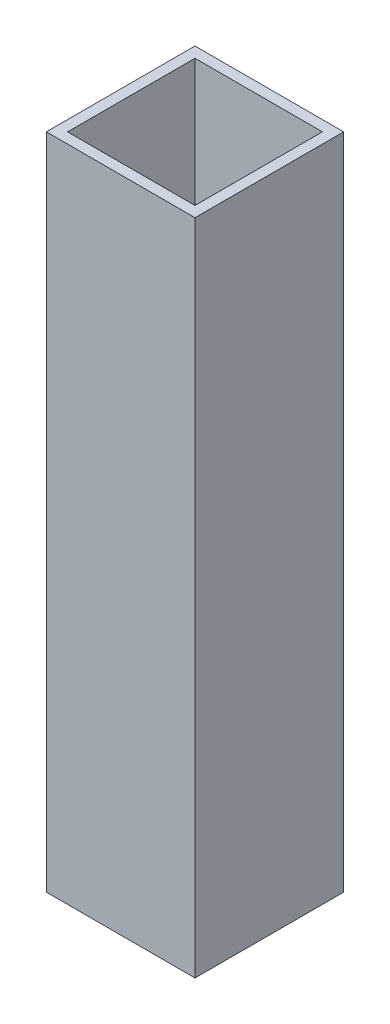
SolidWorks part; units mm, degrees
material "6063-T6"
ref_plane "Front Plane" through (0, 0, 0) normal (0, 0, 1) x (1, 0, 0)
ref_plane "Top Plane" through (0, 0, 0) normal (0, 1, 0) x (1, 0, 0)
ref_plane "Right Plane" through (0, 0, 0) normal (1, 0, 0) x (0, 0, -1)
sketch "Sketch1" plane through (0, 0, 0) normal (0, 1, 0) x (1, 0, 0)
  line L0 (41.275, 3.175) -> (41.275, 41.275)
  line L1 (0, 0) -> (44.45, 0)
  line L2 (0, 0) -> (0, 44.45)
  line L3 (0, 44.45) -> (44.45, 44.45)
  line L4 (44.45, 0) -> (44.45, 44.45)
  line L5 (3.175, 41.275) -> (41.275, 41.275)
  line L6 (3.175, 3.175) -> (3.175, 41.275)
  line L7 (3.175, 3.175) -> (41.275, 3.175)
  dimension "D1" = 44.45
  dimension "D2" = 3.175
extrude "Boss-Extrude1" add sketch "Sketch1" along normal blind 196.85
chamfer "Chamfer1" [suppressed] distance 44.45 angle 45
